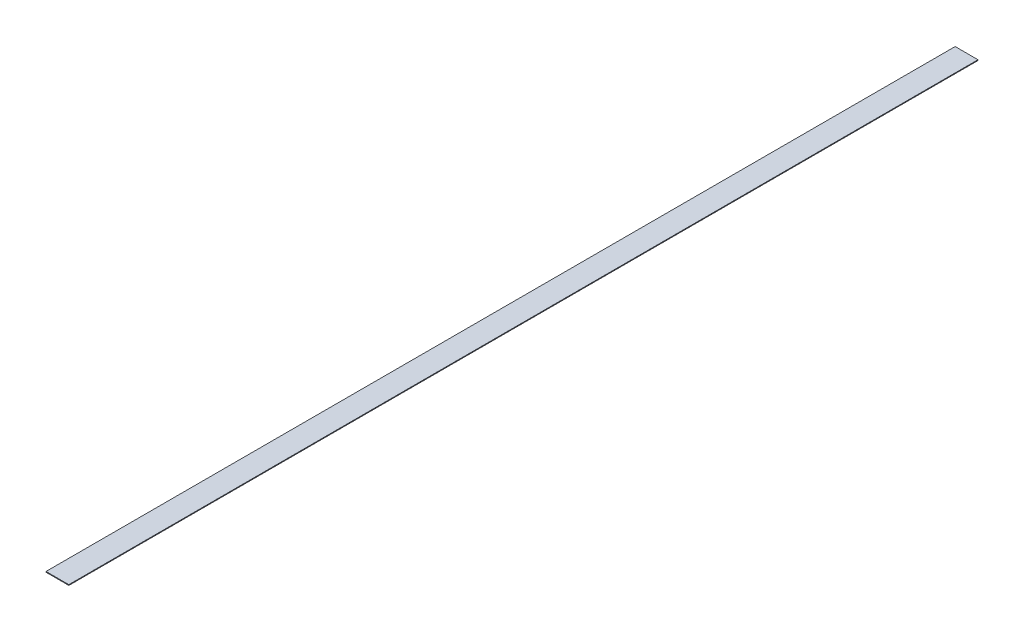
SolidWorks part; units mm, degrees
ref_plane "Front Plane" through (0, 0, 0) normal (0, 0, 1) x (1, 0, 0)
ref_plane "Top Plane" through (0, 0, 0) normal (0, 1, 0) x (1, 0, 0)
ref_plane "Right Plane" through (0, 0, 0) normal (1, 0, 0) x (0, 0, -1)
sketch "Sketch1" plane through (0, 0, 0) normal (0, 1, 0) x (1, 0, 0)
  line L1 (-25.4, -1011.2375) -> (25.4, -1011.2375)
  line L2 (-25.4, -1011.2375) -> (-25.4, 1011.2375)
  line L3 (-25.4, 1011.2375) -> (25.4, 1011.2375)
  line L4 (25.4, -1011.2375) -> (25.4, 1011.2375)
  line L5 (-25.4, -1011.2375) -> (25.4, 1011.2375) construction
  line L6 (-25.4, 1011.2375) -> (25.4, -1011.2375) construction
  point P0 (0, 0)
  dimension "D1" = 50.8
  dimension "D2" = 2022.475
extrude "Boss-Extrude1" add sketch "Sketch1" along normal blind 1.5875
